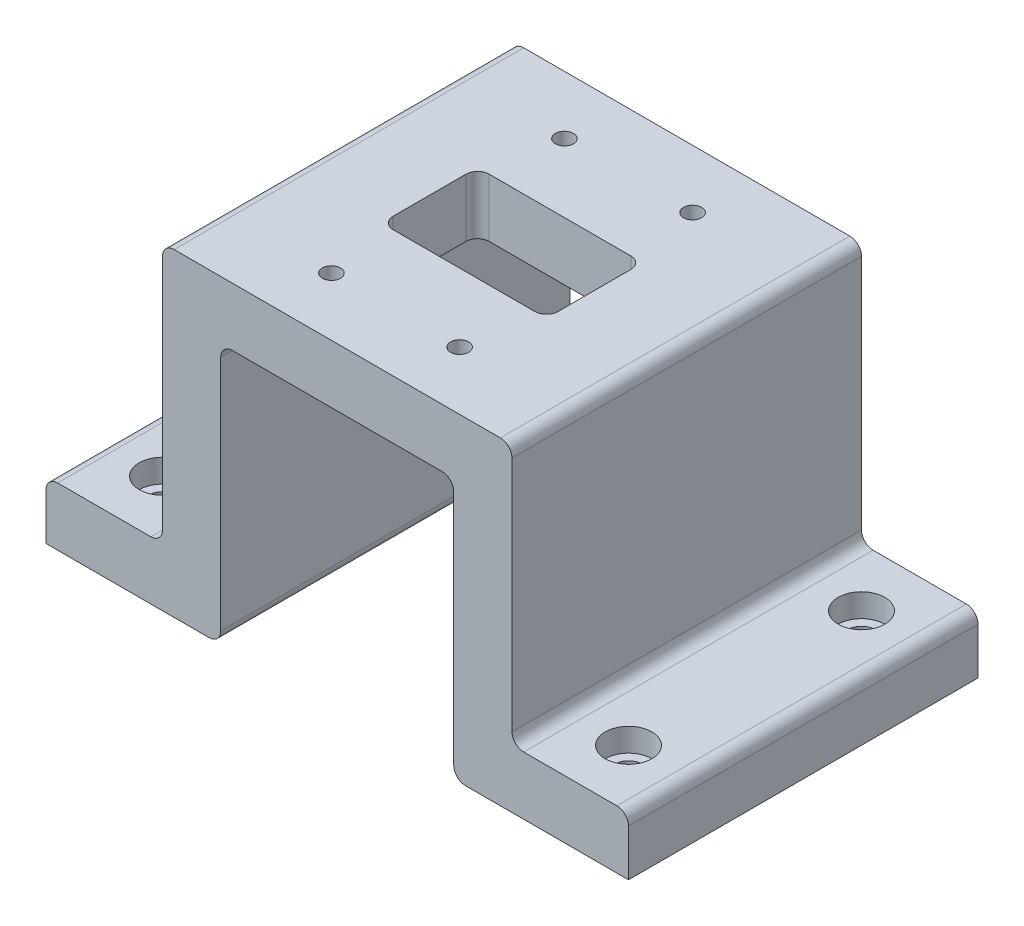
SolidWorks part; units mm, degrees
ref_plane "Front Plane" through (0, 0, 0) normal (0, 0, 1) x (1, 0, 0)
ref_plane "Top Plane" through (0, 0, 0) normal (0, 1, 0) x (1, 0, 0)
ref_plane "Right Plane" through (0, 0, 0) normal (1, 0, 0) x (0, 0, -1)
sketch "Sketch2" plane through (0, 0, 0) normal (0, 1, 0) x (1, 0, 0)
  line L0 (-30, 30) -> (30, 30)
  line L1 (-30, 30) -> (-30, -30)
  line L2 (30, 30) -> (30, -30)
  line L3 (-30, -30) -> (30, -30)
  line L4 (30, -30) -> (-30, 30) construction
  point P0 (0, 0)
  dimension "D1" = 60
  dimension "D2" = 60
extrude "Boss-Extrude1" add sketch "Sketch2" along normal blind 10
sketch "Sketch7" plane through (0, 10, 0) normal (0, 1, 0) x (1, 0, 0)
  line L0 (-14.16, 8.25) -> (14.16, 8.25)
  line L1 (-14.16, 8.25) -> (-14.16, -8.25)
  line L2 (14.16, 8.25) -> (14.16, -8.25)
  line L3 (-14.16, -8.25) -> (14.16, -8.25)
  line L4 (14.16, -8.25) -> (-14.16, 8.25) construction
  point P0 (0, 0)
  dimension "D1" = 28.32
  dimension "D2" = 16.5
extrude "Cut-Extrude2" cut sketch "Sketch7" against normal through all
fillet "Fillet2" radius 2 4 edges at (-14.16, 5, 8.25) (14.16, 5, 8.25) (14.16, 5, -8.25) (-14.16, 5, -8.25)
hole_wizard "CBORE for M2.5 SHCS2" positions "Sketch9" profile "Sketch10" counterbore size "M2.5" standard "ANSI Metric" end condition up to next
sketch "Sketch9" plane through (0, 0, 0) normal (0, -1, 0) x (-1, 0, 0)
  line L0 (-11, 20) -> (11, 20) construction
  line L1 (-11, 20) -> (-11, -20) construction
  line L2 (11, 20) -> (11, -20) construction
  line L3 (-11, -20) -> (11, -20) construction
  line L4 (11, -20) -> (-11, 20) construction
  point P0 (11, -20)
  point P2 (-11, -20)
  point P4 (11, 20)
  point P6 (-11, 20)
  point P50 (0, 0)
  dimension "D1" = 22
  dimension "D2" = 40
sketch "Sketch10" plane through (-11, 0, 20) normal (1, 0, 0) x (0, 0, -1)
  line L0 (0, 0) -> (0, 10)
  line L1 (0, 10) -> (1.55, 10)
  line L3 (1.55, 10) -> (1.55, 2.5)
  line L4 (1.55, 2.5) -> (2.75, 2.5)
  line L5 (2.75, 2.5) -> (2.75, 0)
  line L7 (2.75, 0) -> (0, 0)
  line L11 (0, -6.35) -> (0, 107.95) construction
  dimension "Thru Hole Dia." = 3.1
  dimension "Thru Hole Depth" = 10
  dimension "C'Bore Dia." = 5.5
  dimension "C'Bore Depth" = 2.5
other "Move Face1" face at (11, 2.5, -21.55) face at (-11, 2.5, -21.55) face at (11, 2.5, 18.45) face at (-11, 2.5, 18.45) parameters "D1"=3.5
sketch "Sketch11" plane through (0, 0, -30) normal (0, 0, -1) x (-1, 0, 0)
  line L0 (-30, 0) -> (-20, 0)
  line L1 (-30, 0) -> (-30, -44.7)
  line L2 (-20, 0) -> (-20, -44.7)
  line L3 (-30, -44.7) -> (-20, -44.7)
  line L4 (-30, 0) -> (30, 0) construction
  line L5 (-30, 10) -> (30, 10) construction
  dimension "D1" = 10
  dimension "D2" = 54.7
extrude "Boss-Extrude2" add sketch "Sketch11" against normal up to surface (60 mm away) up to face at (0, 5, 30)
sketch "Sketch12" plane through (0, -44.7, 0) normal (0, -1, 0) x (1, 0, 0)
  line L0 (30, 30) -> (30, -30)
  line L1 (30, 30) -> (50, 30)
  line L2 (30, -30) -> (50, -30)
  line L3 (50, 30) -> (50, -30)
  dimension "D1" = 20
extrude "Boss-Extrude3" add sketch "Sketch12" against normal blind 10
hole_wizard "CBORE for M4 SHCS1" positions "Sketch13" profile "Sketch14" counterbore size "M4" standard "ANSI Metric" end condition up to next
sketch "Sketch13" plane through (0, -34.7, 0) normal (0, 1, 0) x (1, 0, 0)
  line L4 (40, 0) -> (50, 0) construction
  line L5 (50, 30) -> (50, -30) construction
  line L7 (40, 20) -> (40, -20) construction
  line L9 (50, -30) -> (30, -30) construction
  point P0 (40, 20)
  point P2 (40, -20)
  point P24 (40, 0)
  point P28 (40, -30)
  dimension "D1" = 40
sketch "Sketch14" plane through (40, -34.7, -20) normal (1, 0, 0) x (0, 0, 1)
  line L0 (0, 0) -> (0, 10.001)
  line L1 (0, 10.001) -> (2.4, 10.001)
  line L3 (2.4, 10.001) -> (2.4, 4)
  line L4 (2.4, 4) -> (4, 4)
  line L5 (4, 4) -> (4, 0)
  line L7 (4, 0) -> (0, 0)
  line L11 (0, -6.35) -> (0, 107.95) construction
  dimension "Thru Hole Dia." = 4.8
  dimension "Thru Hole Depth" = 10.001
  dimension "C'Bore Dia." = 8
  dimension "C'Bore Depth" = 4
mirror "Mirror1" about plane through (0, 0, 0) normal (1, 0, 0) of "CBORE for M4 SHCS1", "Boss-Extrude3", "Boss-Extrude2"
fillet "Fillet5" radius 2 10 edges at (30, 10, 0) (-30, 10, 0) (-20, -44.7, 0) (20, -44.7, 0) (20, 0, 0) (-20, 0, 0) (30, -34.7, 0) (-30, -34.7, 0) (-50, -34.7, 0) (50, -34.7, 0)
